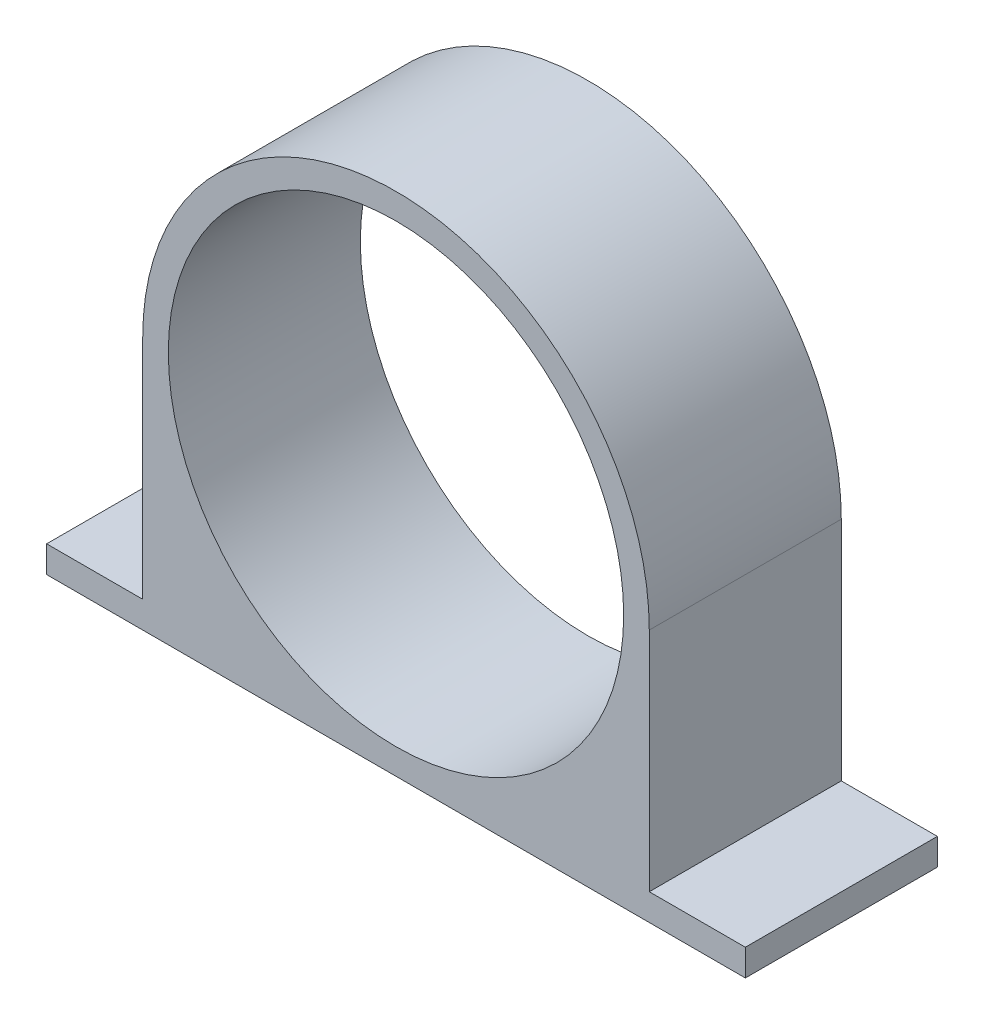
SolidWorks part; units mm, degrees
ref_plane "Front Plane" through (0, 0, 0) normal (0, 0, 1) x (1, 0, 0)
ref_plane "Top Plane" through (0, 0, 0) normal (0, 1, 0) x (1, 0, 0)
ref_plane "Right Plane" through (0, 0, 0) normal (1, 0, 0) x (0, 0, -1)
sketch "Sketch1" plane through (0, 0, 0) normal (0, 0, 1) x (1, 0, 0)
  circle A1 centre (0, 0) radius 33.375
  circle A2 centre (0, 0) radius 30.0075
  dimension "D2" = 66.75
extrude "Boss-Extrude1" add sketch "Sketch1" along normal blind 25.3 contours A2 | A1 A2
sketch "Sketch2" plane through (0, 0, 0) normal (0, 0, -1) x (-1, 0, 0)
  circle A0 centre (0, 0) radius 30
  dimension "D1" = 60
sketch "Base" plane through (0, 0, 0) normal (0, 0, 1) x (1, 0, 0)
  line L0 (0, 0) -> (0, -40.7028) construction
  line L1 (-46.035, -29.8633) -> (46.035, -29.8633)
  line L2 (-46.035, -29.8633) -> (-46.035, -33.375)
  line L3 (-46.035, -33.375) -> (46.035, -33.375)
  line L4 (46.035, -29.8633) -> (46.035, -33.375)
  circle A1 centre (0, 0) radius 33.375 construction
  point P7 (0, 0)
  point P10 (0, -29.8633)
sketch "Dodec" plane through (0, 0, 0) normal (0, 0, 1) x (1, 0, 0)
  line L1 (0, 30) -> (-15, 25.9808) construction
  line L2 (-15, 25.9808) -> (-25.9808, 15) construction
  line L3 (-25.9808, 15) -> (-30, 0) construction
  line L4 (-30, 0) -> (-25.9808, -15) construction
  line L5 (-25.9808, -15) -> (-15, -25.9808) construction
  line L6 (-15, -25.9808) -> (0, -30) construction
  line L7 (0, -30) -> (15, -25.9808) construction
  line L8 (15, -25.9808) -> (25.9808, -15) construction
  line L9 (25.9808, -15) -> (30, 0) construction
  line L10 (30, 0) -> (25.9808, 15) construction
  line L11 (25.9808, 15) -> (15, 25.9808) construction
  line L12 (15, 25.9808) -> (0, 30) construction
  circle A0 centre (0, 0) radius 28.9778 construction
  point P1 (0, 0)
  point P16 (0, 0)
  point P17 (0, 0)
extrude "Boss-Extrude3" add sketch "Base" along normal blind 25.3
sketch "Sketch7" plane through (0, 0, 0) normal (0, 1, 0) x (1, 0, 0)
  line L1 (-33.375, 0) -> (33.375, 0)
  line L2 (-33.375, 0) -> (-33.375, -25.3)
  line L3 (-33.375, -25.3) -> (33.375, -25.3)
  line L4 (33.375, 0) -> (33.375, -25.3)
extrude "Boss-Extrude4" add sketch "Sketch7" against normal blind 33.3
extrude "Cut-Extrude4" cut sketch "Sketch2" against normal blind 33.3
